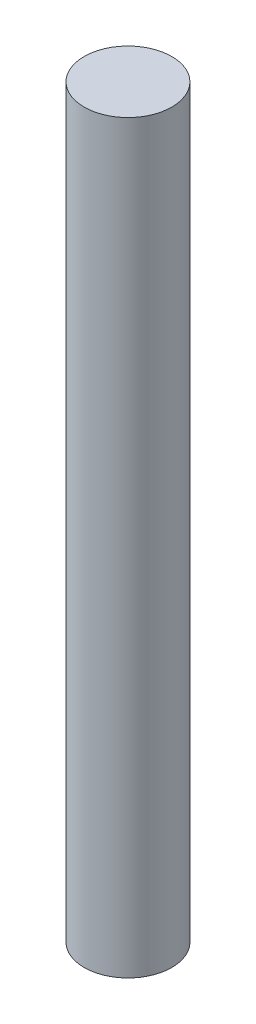
SolidWorks part; units mm, degrees
ref_plane "Plan de face" through (0, 0, 0) normal (0, 0, 1) x (1, 0, 0)
ref_plane "Plan de dessus" through (0, 0, 0) normal (0, 1, 0) x (1, 0, 0)
ref_plane "Plan de droite" through (0, 0, 0) normal (1, 0, 0) x (0, 0, -1)
sketch "Esquisse1" plane through (0, 0, 0) normal (0, 1, 0) x (1, 0, 0)
  circle A0 centre (0, 0) radius 2
  dimension "D1" = 4
extrude "Boss.-Extru.1" add sketch "Esquisse1" along normal blind 34
